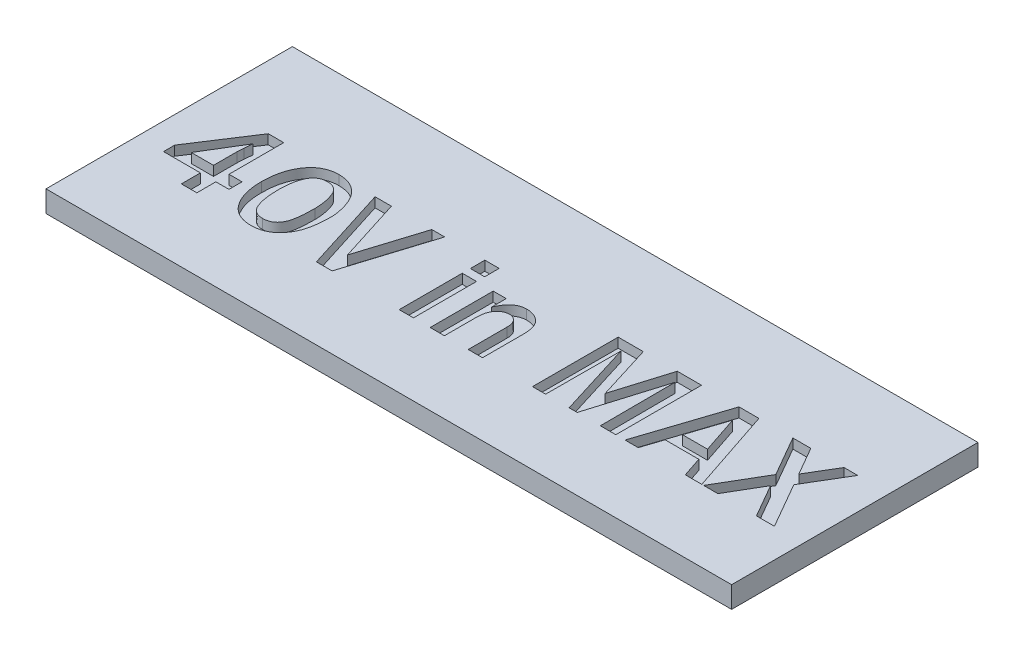
SolidWorks part; units mm, degrees
ref_plane "Front Plane" through (0, 0, 0) normal (0, 0, 1) x (1, 0, 0)
ref_plane "Top Plane" through (0, 0, 0) normal (0, 1, 0) x (1, 0, 0)
ref_plane "Right Plane" through (0, 0, 0) normal (1, 0, 0) x (0, 0, -1)
sketch "Sketch1" plane through (0, 0, 0) normal (0, 1, 0) x (1, 0, 0)
  line L1 (-19.7779, 9.307) -> (12.2221, 9.307)
  line L2 (-19.7779, 9.307) -> (-19.7779, -2.193)
  line L3 (-19.7779, -2.193) -> (12.2221, -2.193)
  line L4 (12.2221, 9.307) -> (12.2221, -2.193)
  dimension "D1" = 11.5
  dimension "D2" = 32
extrude "Boss-Extrude1" add sketch "Sketch1" along normal blind 1
sketch "Sketch2" plane through (0, 1, 0) normal (0, 1, 0) x (1, 0, 0)
  text T0 "40V in MAX" font "Franklin Gothic Medium" height 4
extrude "Cut-Extrude1" cut sketch "Sketch2" against normal blind 0.45
